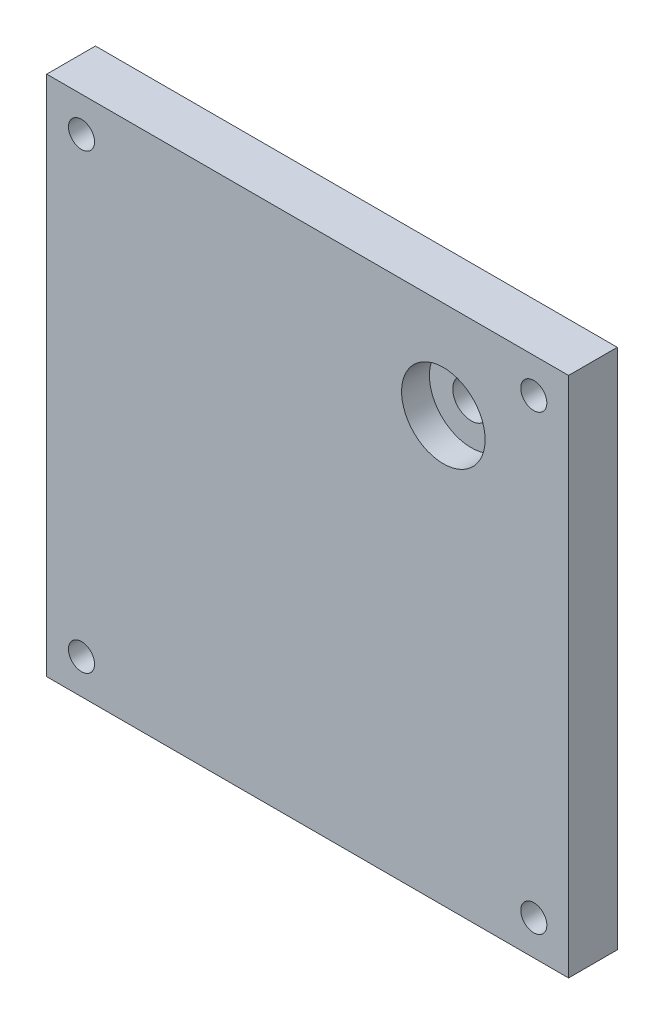
SolidWorks part; units mm, degrees
ref_plane "Front Plane" through (0, 0, 0) normal (0, 0, 1) x (1, 0, 0)
ref_plane "Top Plane" through (0, 0, 0) normal (0, 1, 0) x (1, 0, 0)
ref_plane "Right Plane" through (0, 0, 0) normal (1, 0, 0) x (0, 0, -1)
sketch "Sketch1" plane through (0, 0, 0) normal (0, 0, 1) x (1, 0, 0)
  line L1 (-47.625, -47.625) -> (47.625, -47.625)
  line L2 (-47.625, -47.625) -> (-47.625, 47.625)
  line L3 (-47.625, 47.625) -> (47.625, 47.625)
  line L4 (47.625, -47.625) -> (47.625, 47.625)
  line L5 (-47.625, -47.625) -> (47.625, 47.625) construction
  line L6 (-47.625, 47.625) -> (47.625, -47.625) construction
  point P0 (0, 0)
  dimension "D1" = 95.25
  dimension "D2" = 95.25
extrude "Boss-Extrude1" add sketch "Sketch1" along normal blind 8.89
sketch "Sketch2" plane through (0, 0, 8.89) normal (0, 0, 1) x (1, 0, 0)
  line L0 (47.625, 47.625) -> (-47.625, 47.625) construction
  line L1 (-47.625, -47.625) -> (47.625, -47.625)
  line L2 (-47.625, -47.625) -> (-47.625, 47.625)
  line L3 (-47.625, 47.625) -> (47.625, 47.625)
  line L4 (47.625, -47.625) -> (47.625, 47.625)
  line L5 (-47.625, -47.625) -> (47.625, 47.625) construction
  line L6 (-47.625, 47.625) -> (47.625, -47.625) construction
  line L7 (47.625, -47.625) -> (47.625, 47.625) construction
  line L9 (36.195, -41.275) -> (-36.195, -41.275) construction
  line L10 (41.275, -36.195) -> (41.275, 36.195) construction
  line L11 (36.195, 41.275) -> (-36.195, 41.275) construction
  line L12 (-41.275, -36.195) -> (-41.275, 36.195) construction
  line L13 (41.275, -41.275) -> (-41.275, 41.275) construction
  line L14 (41.275, 41.275) -> (-41.275, -41.275) construction
  arc A0 (-41.275, 36.195) -> (-36.195, 41.275) centre (-41.275, 41.275) ccw construction
  arc A1 (36.195, 41.275) -> (41.275, 36.195) centre (41.275, 41.275) ccw construction
  arc A2 (41.275, -36.195) -> (36.195, -41.275) centre (41.275, -41.275) ccw construction
  arc A3 (-36.195, -41.275) -> (-41.275, -36.195) centre (-41.275, -41.275) ccw construction
  circle A4 centre (-41.275, 41.275) radius 2.3812
  circle A5 centre (41.275, 41.275) radius 2.3812
  circle A6 centre (41.275, -41.275) radius 2.3812
  circle A7 centre (-41.275, -41.275) radius 2.3812
  point P0 (0, 0)
  point P10 (0, 0)
  dimension "D2" = 5.08
  dimension "D3" = 4.7625
  dimension "D1" = 6.35
extrude "Cut-Extrude2" cut sketch "Sketch2" against normal through all flip side to cut
ref_plane "Plane1" through (0, 0, 8.89) normal (0, 0, 1) x (1, 0, 0)
sketch "Sketch3" plane through (0, 0, 8.89) normal (0, 0, 1) x (1, 0, 0)
  line L0 (47.625, -47.625) -> (47.625, 47.625) construction
  line L1 (47.625, 47.625) -> (-47.625, 47.625) construction
  circle A0 centre (24.765, 29.845) radius 7.62
  dimension "D1" = 15.24
  dimension "D2" = 22.86
  dimension "D3" = 17.78
extrude "Cut-Extrude3" cut sketch "Sketch3" against normal blind 5.08 contours A0
sketch "Sketch4" plane through (0, 0, 3.81) normal (0, 0, 1) x (1, 0, 0)
  circle A0 centre (24.765, 29.845) radius 3.3655
  dimension "D1" = 6.731
extrude "Cut-Extrude4" cut sketch "Sketch4" against normal through all
